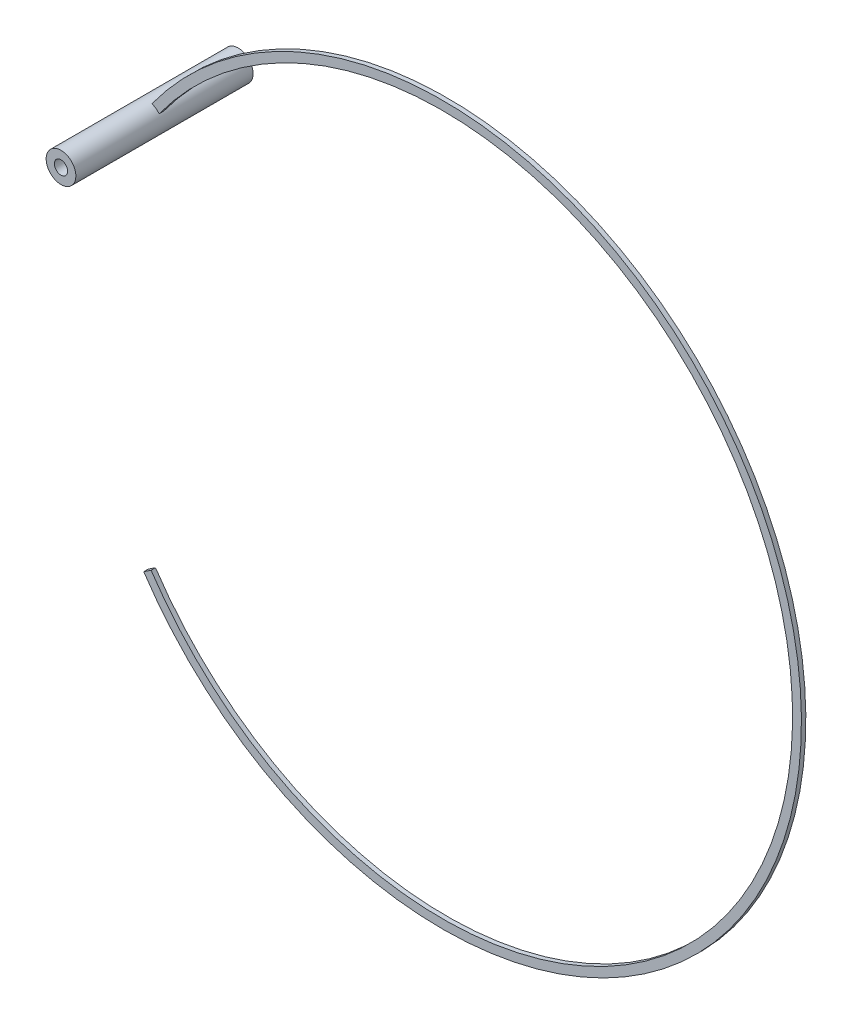
SolidWorks part; units mm, degrees
ref_plane "Front Plane" through (0, 0, 0) normal (0, 0, 1) x (1, 0, 0)
ref_plane "Top Plane" through (0, 0, 0) normal (0, 1, 0) x (1, 0, 0)
ref_plane "Right Plane" through (0, 0, 0) normal (1, 0, 0) x (0, 0, -1)
sketch "Sketch1" plane through (0, 0, 0) normal (0, 0, 1) x (1, 0, 0)
  circle A0 centre (-12.4954, 27.3398) radius 1.6753
  circle A1 centre (-12.4954, 27.3398) radius 0.75
extrude "Boss-Extrude1" add sketch "Sketch1" along normal mid plane 20
sketch "Sketch2" plane through (0, 0, 0) normal (0, 0, 1) x (1, 0, 0)
  arc A0 (-12.4954, 27.3398) -> (-12.4954, -16.9697) centre (20.8088, 5.1851) cw
  dimension "D1" = 40
sketch "Sketch3" plane through (-12.4954, 27.3398, 0) normal (0.5539, 0.8326, 0) x (0, 0, 1)
  line L1 (-0.2486, -0.5) -> (0.2486, -0.5)
  line L2 (-0.2486, -0.5) -> (-0.2486, 0.5)
  line L3 (-0.2486, 0.5) -> (0.2486, 0.5)
  line L4 (0.2486, -0.5) -> (0.2486, 0.5)
  line L5 (-0.2486, -0.5) -> (0.2486, 0.5) construction
  line L6 (-0.2486, 0.5) -> (0.2486, -0.5) construction
sweep "Sweep1" add profiles "Sketch3" path "Sketch2"
